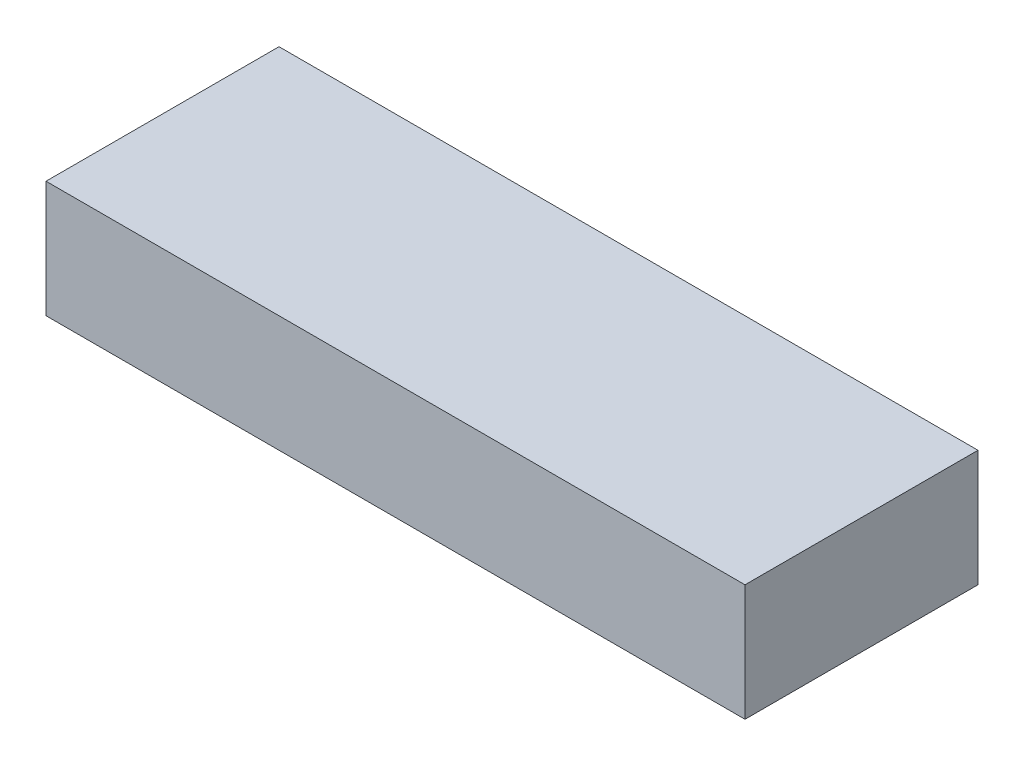
SolidWorks part; units mm, degrees
material "Acrylic (Medium-high impact)"
ref_plane "Front Plane" through (0, 0, 0) normal (0, 0, 1) x (1, 0, 0)
ref_plane "Top Plane" through (0, 0, 0) normal (0, 1, 0) x (1, 0, 0)
ref_plane "Right Plane" through (0, 0, 0) normal (1, 0, 0) x (0, 0, -1)
sketch "Sketch1" plane through (0, 0, 0) normal (0, 1, 0) x (1, 0, 0)
  line L1 (-19.05, -6.35) -> (19.05, -6.35)
  line L2 (-19.05, -6.35) -> (-19.05, 6.35)
  line L3 (-19.05, 6.35) -> (19.05, 6.35)
  line L4 (19.05, -6.35) -> (19.05, 6.35)
  line L5 (-19.05, -6.35) -> (19.05, 6.35) construction
  line L6 (-19.05, 6.35) -> (19.05, -6.35) construction
  point P0 (0, 0)
extrude "Boss-Extrude1" add sketch "Sketch1" along normal blind 6.35
sketch "Sketch2" plane through (0, 6.35, 0) normal (0, 1, 0) x (1, 0, 0)
  text T0 "<b>MOTOR 2</b>\r\n" font "Century Gothic" height in points 16
extrude "Boss-Extrude2" add sketch "Sketch2" against normal blind 0.508 separate body
